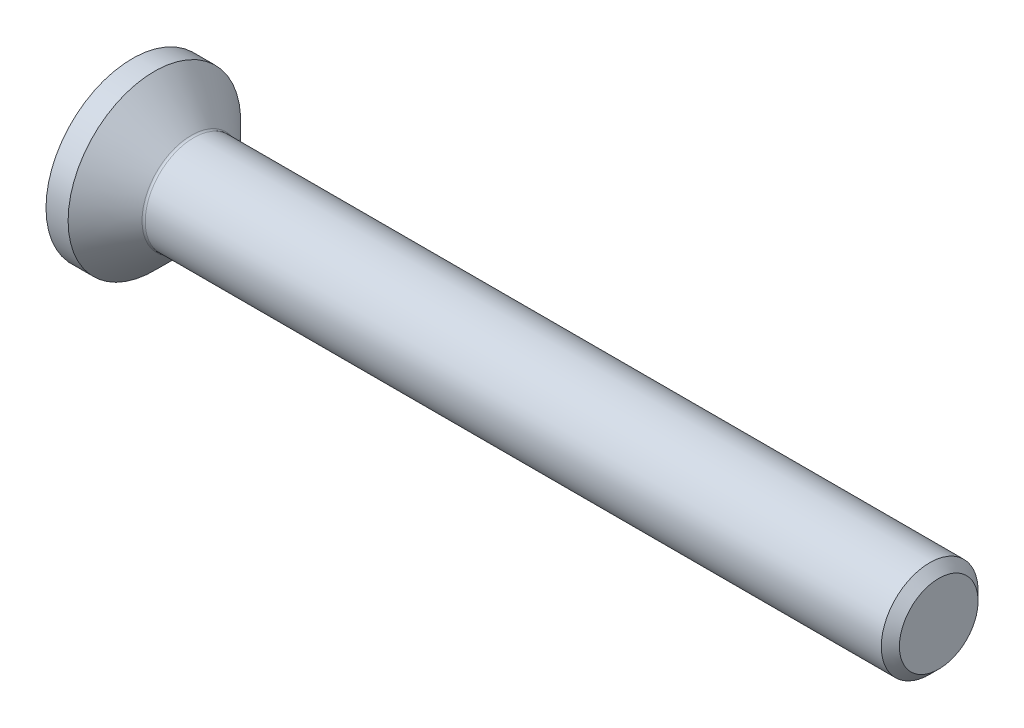
SolidWorks part; units mm, degrees
ref_plane "Plane1" through (0, 0, 0) normal (0, 0, 1) x (1, 0, 0)
ref_plane "Plane2" through (0, 0, 0) normal (0, 1, 0) x (1, 0, 0)
ref_plane "Plane3" through (0, 0, 0) normal (1, 0, 0) x (0, 0, -1)
sketch "BodySke" plane through (0, 0, 0) normal (0, 0, 1) x (1, 0, 0)
  line L0 (0, 0) -> (0, 2.675)
  line L1 (0.685, 2.675) -> (1.86, 1.5)
  line L2 (0, 2.675) -> (0.685, 2.675)
  line L3 (1.86, 1.5) -> (24.7195, 1.5)
  line L4 (25, 1.2195) -> (25, 0)
  line L5 (25, 0) -> (0, 0)
  line L6 (0, 0) -> (127, 0) construction
  line L7 (0.685, -2.675) -> (1.86, -1.5) construction
  line L8 (25, 1.2195) -> (24.7195, 1.5)
  line L9 (0, -2.675) -> (0.685, -2.675) construction
  line L10 (25, -1.2195) -> (24.7195, -1.5) construction
  line L11 (2.36, 7.85) -> (2.36, -14.375) construction
  line L12 (0, 19.05) -> (0, -3.175) construction
  dimension "D1" = 0.685
  dimension "Diameter" = 3
  dimension "Head_ht" = 1.86
  dimension "Length" = 25
  dimension "Body_ch_ang" = 45
  dimension "Head_dia" = 5.35
  dimension "Minor_dia" = 2.439
  dimension "Head_ang" = 90
  dimension "Advance" = 0.5
  dimension "Thread_nom" = 25
revolve "BaseBody" add sketch "BodySke" angle 360 about L6
cosmetic thread "ThreadCosmetic" parameters "Thread_length"=22.14, "Thread_minor"=2.439
fillet "Fillet1" radius 0.1 1 edges at (1.86, 0, 1.5)
sketch "Sketch2" plane through (0, 0, 0) normal (0, 0, 1) x (1, 0, 0)
  line L0 (0, 1) -> (1.1, 1)
  line L1 (1.1, 1) -> (1.6774, 0)
  line L2 (0, 0) -> (127, 0) construction
  line L3 (1.6774, 0) -> (0, 0)
  line L4 (0, 0) -> (0, 1)
  line L5 (0, -1) -> (1.1, -1) construction
  line L6 (0, 0) -> (47.625, 0) construction
  line L8 (0, 2.675) -> (0, -2.675) construction
  dimension "D2" = 60
  dimension "PreBroach_depth" = 1.1
  dimension "PreBroach_dia" = 2
revolve "PreBroach" cut sketch "Sketch2" angle 360 about L6
sketch "Sketch3" plane through (0, 0, 0) normal (-1, 0, 0) x (0, 0, 1)
  line L0 (-1, -0.5774) -> (-1, 0.5774)
  line L1 (-1, 0.5774) -> (0, 1.1547)
  line L2 (0, 1.1547) -> (1, 0.5774)
  line L3 (1, 0.5774) -> (1, -0.5774)
  line L4 (1, -0.5774) -> (0, -1.1547)
  line L5 (0, -1.1547) -> (-1, -0.5774)
  dimension "D1" = 1
  dimension "D2" = 1
  dimension "D3" = 2
  dimension "Hex_size" = 2
extrude "Hex" cut sketch "Sketch3" against normal blind 1.1
sketch "ThdSchSke" plane through (0, 0, 0) normal (0, 0, 1) x (1, 0, 0)
  line L0 (2.86, -1.2195) -> (2.6636, -1.5)
  line L1 (2.86, -1.2195) -> (3.0564, -1.5)
  line L2 (3.0564, -1.5) -> (3.0564, -1.875)
  line L3 (-3.175, 0) -> (5.1513, 0) construction
  line L4 (0, 2.675) -> (0, -2.675) construction
  line L5 (3.0564, -1.875) -> (2.6636, -1.875)
  line L6 (2.6636, -1.875) -> (2.6636, -1.5)
  dimension "Thread_minor" = 2.439
  dimension "Diameter" = 3
  dimension "Start" = 2.86
  dimension "SideAngle" = 55
  dimension "VeeAngle" = 70
  dimension "Overcut" = 3.75
revolve "ThreadSchematic" [suppressed] cut sketch "ThdSchSke" angle 360 about L3
pattern_linear "ThdSchPat" [suppressed]
equation "\"Thread_minor@ThreadCosmetic\"  =  \"Minor_dia@BodySke\""
equation "\"D1@Sketch3\" = \"Hex_size@Sketch3\" / 2"
equation "\"D2@Sketch3\" = \"D1@Sketch3\""
equation "\"D3@Sketch3\" = \"Hex_size@Sketch3\""
equation "\"Thread_length@ThreadCosmetic\" = ((sgn( (\"Length@BodySke\" - \"Advance@BodySke\" * 2.0 - \"Head_ht@BodySke\" ) - \"Thread_nom@BodySke\" )-1)*( (\"Length@BodySke\" - \"Advance@BodySke\" * 2.0 - \"Head_ht@BodySke\" ) - \"Thread_nom@BodySke\" ))/-2+ \"Thread_nom@BodySke\""
equation "\"Thread_minor@ThdSchSke\" = \"Minor_dia@BodySke\""
equation "\"Diameter@ThdSchSke\" = \"Diameter@BodySke\""
equation "\"Overcut@ThdSchSke\" = \"Diameter@BodySke\" * 1.25"
equation "\"Start@ThdSchSke\" = 0.000001 + \"Length@BodySke\" - \"Thread_length@ThreadCosmetic\"  '---Countersunk---"
equation "\"Num_threads@ThdSchPat\" = int( \"Thread_length@ThreadCosmetic\" / \"Advance@BodySke\" + 0.999 )  + 1"
equation "\"Advance@ThdSchPat\" = \"Thread_length@ThreadCosmetic\" /  (\"Num_threads@ThdSchPat\" - 1) 'relax it"
equation "\"Num_threads@ThdSchPat\" = \"Num_threads@ThdSchPat\" - sgn( \"Num_threads@ThdSchPat\" - 1) '---chamfered tips only---"
